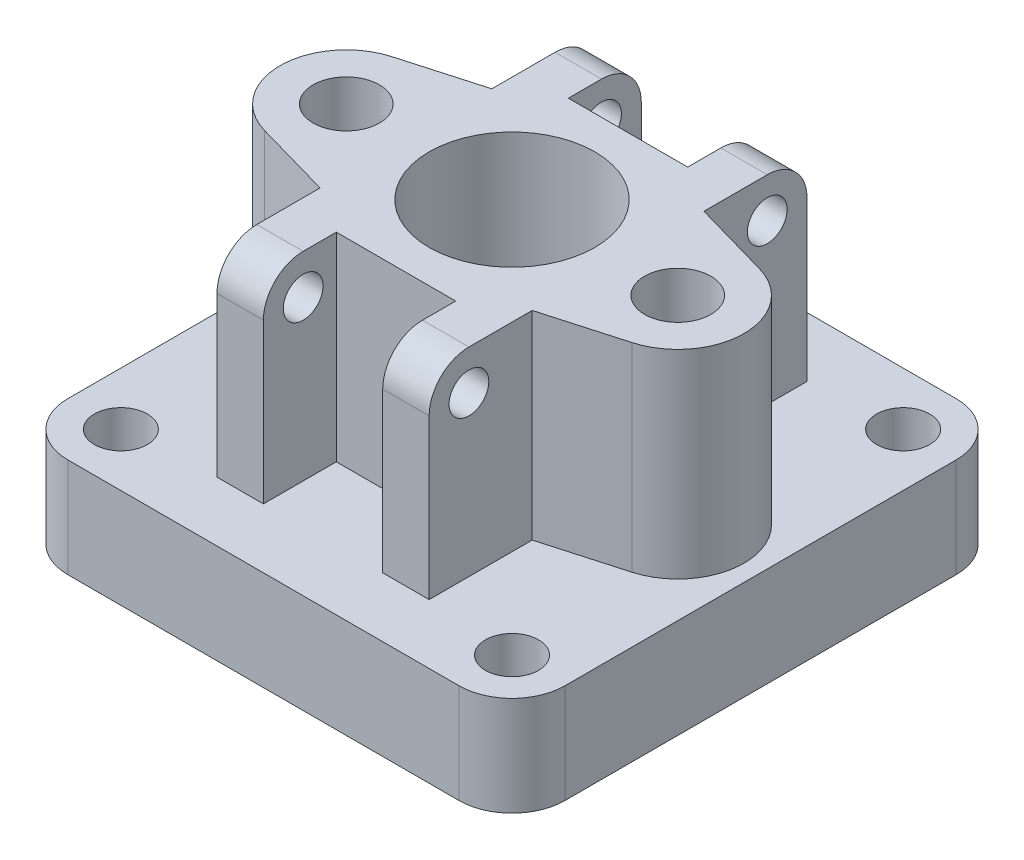
SolidWorks part; units mm, degrees
material "Hierro dúctil"
ref_plane "Alzado" through (0, 0, 0) normal (0, 0, 1) x (1, 0, 0)
ref_plane "Planta" through (0, 0, 0) normal (0, 1, 0) x (1, 0, 0)
ref_plane "Vista lateral" through (0, 0, 0) normal (1, 0, 0) x (0, 0, -1)
sketch "Croquis1" plane through (0, 0, 0) normal (0, 1, 0) x (1, 0, 0)
  line L1 (-37.5, 37.5) -> (37.5, 37.5)
  line L2 (-37.5, 37.5) -> (-37.5, -37.5)
  line L3 (-37.5, -37.5) -> (37.5, -37.5)
  line L4 (37.5, 37.5) -> (37.5, -37.5)
  line L5 (-37.5, 37.5) -> (37.5, -37.5) construction
  line L6 (-37.5, -37.5) -> (37.5, 37.5) construction
  point P0 (0, 0)
  dimension "D1" = 75
  dimension "D2" = 75
extrude "Saliente-Extruir1" add sketch "Croquis1" along normal blind 15
fillet "Redondeo1" radius 8 4 edges at (37.5, 7.5, -37.5) (-37.5, 7.5, -37.5) (-37.5, 7.5, 37.5) (37.5, 7.5, 37.5)
sketch "Croquis2" plane through (0, 15, 0) normal (0, 1, 0) x (1, 0, 0)
  arc A8 (-37.5, -29.5) -> (-29.5, -37.5) centre (-29.5, -29.5) ccw construction
  circle A9 centre (-29.5, 29.5) radius 4
  circle A10 centre (-29.5, -29.5) radius 4
  circle A11 centre (29.5, 29.5) radius 4
  circle A12 centre (29.5, -29.5) radius 4
  dimension "D1" = 4
  dimension "D2" = 59
extrude "Cortar-Extruir1" cut sketch "Croquis2" against normal blind 15
sketch "Croquis3" plane through (0, 15, 0) normal (0, 1, 0) x (1, 0, 0)
  line L0 (-16, -28.5) -> (-9, -28.5)
  line L2 (-16, 28.5) -> (-16, 12.9534)
  line L4 (16, 28.5) -> (16, 12.9534)
  line L5 (-16, 28.5) -> (16, -28.5) construction
  line L6 (-16, -28.5) -> (16, 28.5) construction
  line L7 (-9, -28.5) -> (-9, -17.5)
  line L8 (-16, 28.5) -> (-9, 28.5)
  line L9 (16, 28.5) -> (9, 28.5)
  line L10 (16, -28.5) -> (9, -28.5)
  line L11 (-9, 28.5) -> (-9, 17.5)
  line L12 (9, 28.5) -> (9, 17.5)
  line L13 (9, -28.5) -> (9, -17.5)
  line L14 (-9, 17.5) -> (9, 17.5)
  line L15 (-9, -17.5) -> (9, -17.5)
  line L16 (0, -37.5) -> (0, -25) construction
  line L17 (-29.5, -37.5) -> (29.5, -37.5) construction
  line L18 (29.5, 37.5) -> (-29.5, 37.5) construction
  line L20 (16, 12.9534) -> (27.7334, 9.6192)
  line L21 (-16, -12.9534) -> (-27.7334, -9.6192)
  line L23 (0, -17.5) -> (0, 37.5) construction
  line L24 (-16, 12.9534) -> (-27.7334, 9.6192)
  line L25 (16, -12.9534) -> (27.7334, -9.6192)
  line L26 (-16, -12.9534) -> (-16, -28.5)
  line L27 (16, -12.9534) -> (16, -28.5)
  arc A5 (27.7334, -9.6192) -> (27.7334, 9.6192) centre (25, 0) ccw
  arc A6 (-27.7334, 9.6192) -> (-27.7334, -9.6192) centre (-25, 0) ccw
  point P1 (0, 0)
  dimension "D1" = 57
  dimension "D3" = 20
  dimension "D4" = 32
  dimension "D5" = 7
  dimension "D6" = 7
  dimension "D7" = 17.5
  dimension "D8" = 17.5
extrude "Saliente-Extruir2" add sketch "Croquis3" along normal blind 30
sketch "Croquis4" plane through (0, 0, 0) normal (0, -1, 0) x (-1, 0, 0)
  circle A0 centre (0, 0) radius 23
  dimension "D1" = 46
fillet "Redondeo2" radius 6 4 edges at (12.5, 45, -28.5) (-12.5, 45, -28.5) (-12.5, 45, 28.5) (12.5, 45, 28.5)
sketch "Croquis5" plane through (16, 0, 0) normal (1, 0, 0) x (0, 0, -1)
  circle A0 centre (-22.5, 39) radius 3
  arc A1 (-22.5, 45) -> (-28.5, 39) centre (-22.5, 39) ccw construction
  circle A2 centre (22.5, 39) radius 3
  arc A3 (28.5, 39) -> (22.5, 45) centre (22.5, 39) ccw construction
  dimension "D1" = 6
  dimension "D2" = 6
extrude "Cortar-Extruir2" cut sketch "Croquis5" against normal through all
sketch "Croquis6" plane through (0, 45, 0) normal (0, 1, 0) x (1, 0, 0)
  circle A0 centre (0, 0) radius 10
  circle A1 centre (0, 0) radius 12.5
  circle A2 centre (-25, 0) radius 5
  arc A3 (-27.7334, 9.6192) -> (-27.7334, -9.6192) centre (-25, 0) ccw construction
  circle A4 centre (25, 0) radius 5
  arc A5 (27.7334, -9.6192) -> (27.7334, 9.6192) centre (25, 0) ccw construction
  dimension "D1" = 20
  dimension "D2" = 25
  dimension "D3" = 10
  dimension "D4" = 10
extrude "Cortar-Extruir4" cut sketch "Croquis6" against normal blind 30 contours A2 | A4 | A0
sketch "Croquis8" plane through (0, 45, 0) normal (0, 1, 0) x (1, 0, 0)
  circle A0 centre (0, 0) radius 12.5
  dimension "D1" = 25
extrude "Saliente-Extruir4" add sketch "Croquis4" along normal blind 5
extrude "Cortar-Extruir6" cut sketch "Croquis8" against normal through all
